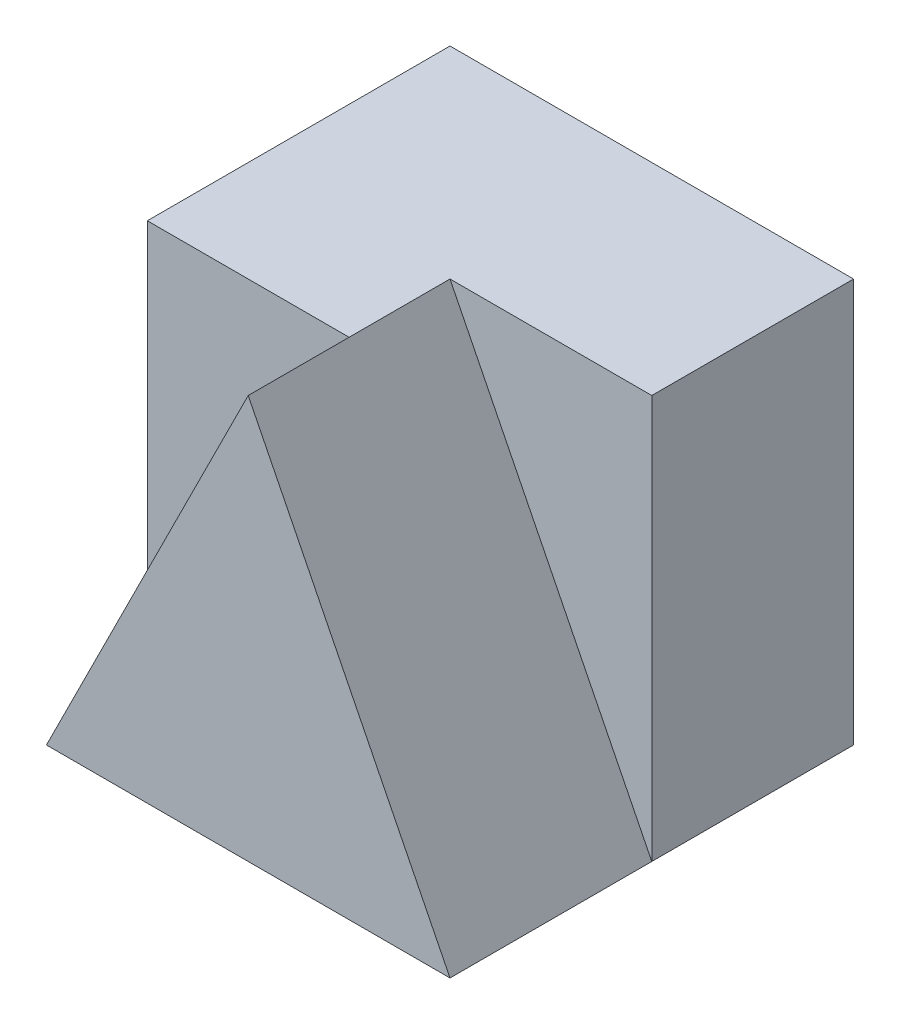
SolidWorks part; units mm, degrees
ref_plane "Front" through (0, 0, 0) normal (0, 0, 1) x (1, 0, 0)
ref_plane "Top" through (0, 0, 0) normal (0, 1, 0) x (1, 0, 0)
ref_plane "Right" through (0, 0, 0) normal (1, 0, 0) x (0, 0, -1)
sketch "Sketch1" plane through (0, 0, 0) normal (0, 1, 0) x (1, 0, 0)
  line L1 (-2, -2) -> (2, -2)
  line L2 (-2, -2) -> (-2, 2)
  line L3 (-2, 2) -> (2, 2)
  line L4 (2, -2) -> (2, 2)
  line L5 (-2, -2) -> (2, 2) construction
  line L6 (-2, 2) -> (2, -2) construction
  point P0 (0, 0)
  dimension "D1" = 4
  dimension "D2" = 4
extrude "Boss-Extrude1" add sketch "Sketch1" along normal blind 4
sketch "Sketch4" plane through (0, 0, 2) normal (0, 0, 1) x (1, 0, 0)
  line L0 (0, 4) -> (2, 4)
  line L1 (-2, 4) -> (2, 4) construction
  line L2 (2, 4) -> (2, 0)
  line L3 (2, 0) -> (0, 4)
extrude "Cut-Extrude1" cut sketch "Sketch4" against normal blind 2
sketch "Sketch5" plane through (0, 0, 2) normal (0, 0, 1) x (1, 0, 0)
  line L0 (0, 4) -> (-2, 0)
  line L1 (-2, 0) -> (-2, 4)
  line L2 (-2, 4) -> (0, 4)
extrude "Cut-Extrude2" cut sketch "Sketch5" against normal blind 1
